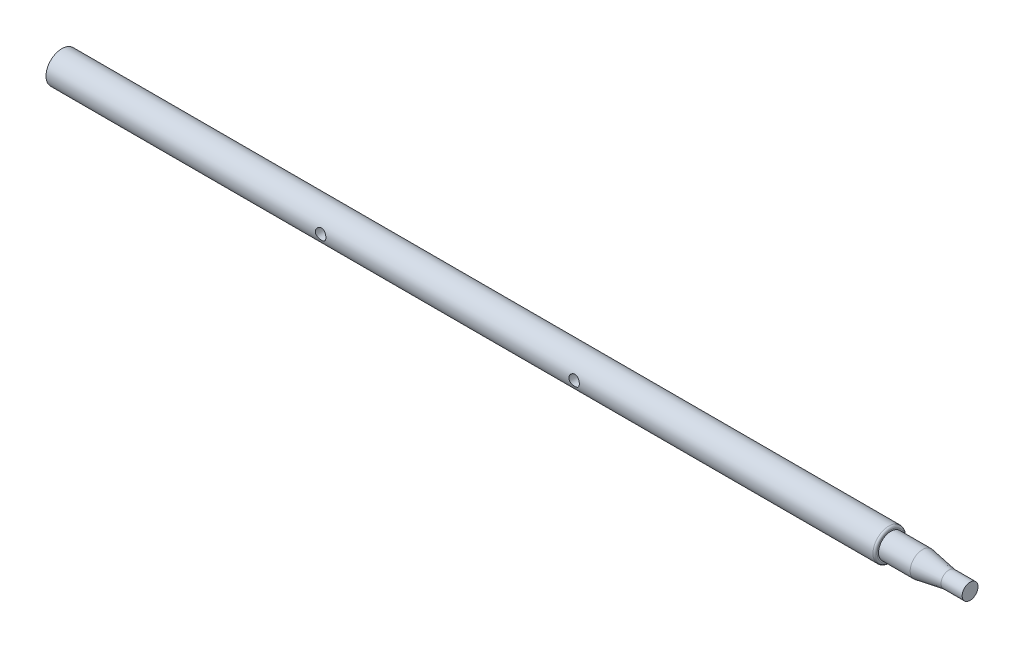
SolidWorks part; units mm, degrees
ref_plane "Front Plane" through (0, 0, 0) normal (0, 0, 1) x (1, 0, 0)
ref_plane "Top Plane" through (0, 0, 0) normal (0, 1, 0) x (1, 0, 0)
ref_plane "Right Plane" through (0, 0, 0) normal (1, 0, 0) x (0, 0, -1)
sketch "Sketch1" plane through (0, 0, 0) normal (0, 0, 1) x (1, 0, 0)
  line L0 (-782.7723, 0) -> (77.2277, 0) construction
  line L1 (-782.7723, 0) -> (-782.7723, 15)
  line L2 (-782.7723, 15) -> (2.2277, 15)
  line L3 (77.2277, 0) -> (77.2277, 7.5)
  line L4 (77.2277, 7.5) -> (57.2277, 7.5)
  line L5 (57.2277, 7.5) -> (32.2277, 11.7327)
  line L6 (32.2277, 11.7327) -> (2.2277, 11.7327)
  line L7 (2.2277, 11.7327) -> (2.2277, 15)
  line L8 (-782.7723, 0) -> (77.2277, 0)
  dimension "D1" = 15
  dimension "D2" = 860
  dimension "D3" = 20
  dimension "D4" = 25
  dimension "D5" = 30
revolve "Revolve1" add sketch "Sketch1" angle 360 about L0
fillet "Fillet1" radius 2 1 edges at (2.2277, 0, 15)
sketch "Sketch2" plane through (0, 0, 0) normal (0, 0, 1) x (1, 0, 0)
  line L0 (-782.7723, 15) -> (-782.7723, -15) construction
  circle A0 centre (-522.7723, 0) radius 5
  circle A1 centre (-282.7723, 0) radius 5
  dimension "D2" = 10
  dimension "D3" = 10
  dimension "D1" = 260
  dimension "D4" = 500
extrude "Cut-Extrude1" cut sketch "Sketch2" against normal through all both and the other way through all
